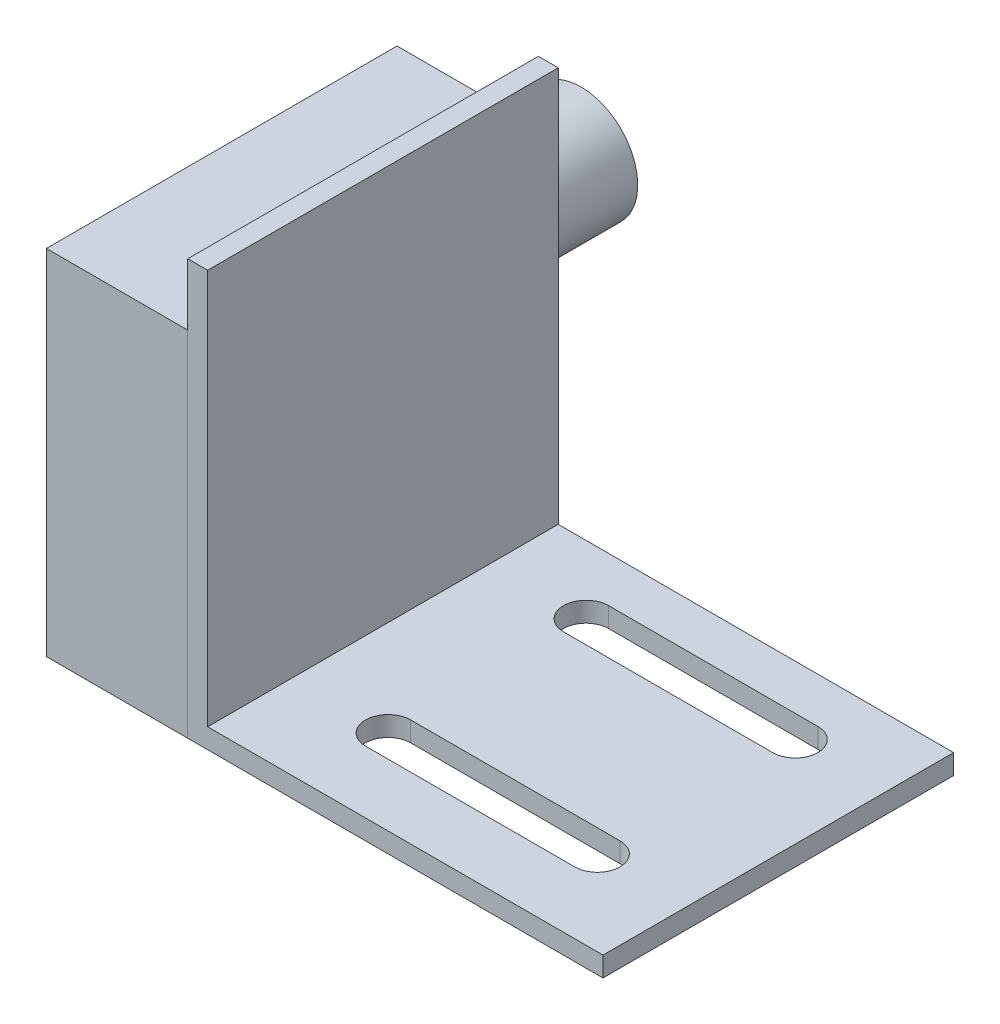
SolidWorks part; units mm, degrees
ref_plane "Front Plane" through (0, 0, 0) normal (0, 0, 1) x (1, 0, 0)
ref_plane "Top Plane" through (0, 0, 0) normal (0, 1, 0) x (1, 0, 0)
ref_plane "Right Plane" through (0, 0, 0) normal (1, 0, 0) x (0, 0, -1)
sketch "Sketch1" plane through (0, 0, 0) normal (0, 0, 1) x (1, 0, 0)
  line L9 (0, 0) -> (0, 37.2983)
  line L10 (0, 37.2983) -> (1.7849, 37.2983)
  line L11 (1.7849, 37.2983) -> (1.7849, 1.7849)
  line L12 (1.7849, 1.7849) -> (37.2983, 1.7849)
  line L13 (37.2983, 1.7849) -> (37.2983, 0)
  line L14 (37.2983, 0) -> (0, 0)
  dimension "D1" = 1.7849
  dimension "D2" = 1.7849
  dimension "D3" = 37.2983
  dimension "D4" = 37.2983
extrude "Boss-Extrude1" add sketch "Sketch1" along normal mid plane 31.496
sketch "Sketch2" plane through (0, 0, 0) normal (-1, 0, 0) x (0, 0, 1)
  line L0 (-15.748, 37.2983) -> (-15.748, 0) construction
  line L1 (15.748, 0) -> (-15.748, 0)
  line L2 (15.748, 0) -> (15.748, 31.75)
  line L3 (15.748, 31.75) -> (-15.748, 31.75)
  line L4 (-15.748, 0) -> (-15.748, 31.75)
  dimension "D1" = 31.75
extrude "Boss-Extrude2" add sketch "Sketch2" along normal blind 12.7 separate body
sketch "Sketch4" plane through (0, 0, -15.748) normal (0, 0, -1) x (-1, 0, 0)
  line L0 (12.7, 31.75) -> (12.7, 0) construction
  line L1 (12.7, 31.75) -> (0, 31.75) construction
  circle A0 centre (6.3209, 21.59) radius 5.08
  dimension "D3" = 10.16
  dimension "D1" = 6.3791
  dimension "D2" = 10.16
extrude "Boss-Extrude3" add sketch "Sketch4" along normal blind 10.16
sketch "Sketch6" plane through (0, 1.7849, 0) normal (0, 1, 0) x (1, 0, 0)
  line L0 (29.1703, 11.684) -> (10.3743, 11.684)
  line L1 (29.1703, 7.62) -> (10.3743, 7.62)
  line L3 (0, 15.748) -> (37.2983, 15.748) construction
  line L5 (37.2983, -15.748) -> (37.2983, 15.748) construction
  arc A0 (29.1703, 7.62) -> (29.1703, 11.684) centre (29.1703, 9.652) ccw
  arc A2 (10.3743, 11.684) -> (10.3743, 7.62) centre (10.3743, 9.652) ccw
  point P3 (0, 0)
  dimension "D1" = 4.064
  dimension "D2" = 4.064
  dimension "D4" = 18.796
  dimension "D7" = 8.128
extrude "Cut-Extrude1" cut sketch "Sketch6" against normal through all
pattern_linear "LPattern1" count 2 spacing 17.78 along (0, 0, 1) of "Cut-Extrude1"
equation "\"D2@Sketch1\"=\"D1@Sketch1\""
equation "\"D4@Sketch1\"=\"D3@Sketch1\""
